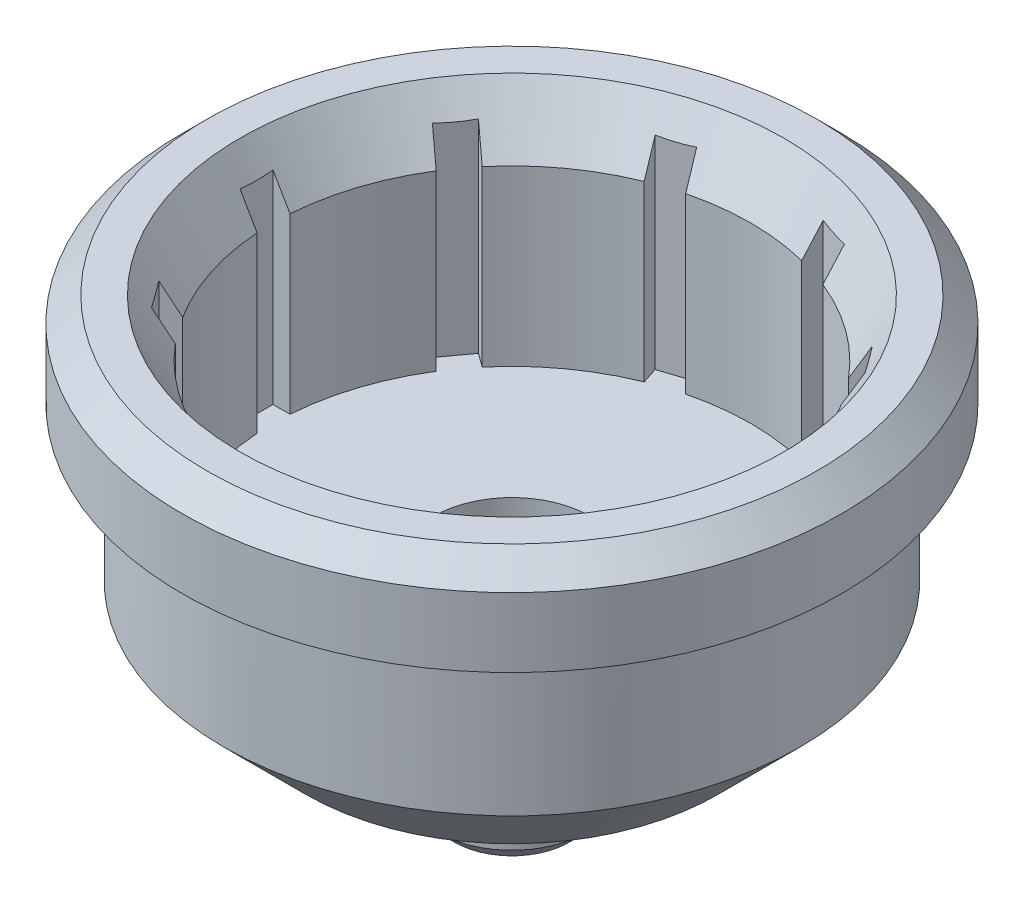
SolidWorks part; units mm, degrees
ref_plane "Front Plane" through (0, 0, 0) normal (0, 0, 1) x (1, 0, 0)
ref_plane "Top Plane" through (0, 0, 0) normal (0, 1, 0) x (1, 0, 0)
ref_plane "Right Plane" through (0, 0, 0) normal (1, 0, 0) x (0, 0, -1)
sketch "Sketch1" plane through (0, 0, 0) normal (0, 0, 1) x (1, 0, 0)
  line L0 (0, 0) -> (-2.5, 0) construction
  line L1 (-2.5, 0) -> (-2.5, 9)
  line L2 (-2.5, 9) -> (-4.75, 9)
  line L3 (-4.75, 9) -> (-4.75, 13)
  line L4 (-4.75, 13) -> (-14.5, 13)
  line L5 (-14.5, 13) -> (-14.5, 27)
  line L6 (-14.5, 27) -> (-20, 27)
  line L7 (-20, 27) -> (-20, 21.3)
  line L8 (-20, 21.3) -> (-17.5, 21.3)
  line L9 (-17.5, 21.3) -> (-17.5, 7)
  line L10 (-17.5, 7) -> (-6.5, 7)
  line L11 (-6.5, 7) -> (-6.5, 6)
  line L12 (-6.5, 6) -> (-4.5, 6)
  line L13 (-4.5, 6) -> (-4.5, 0)
  line L14 (-4.5, 0) -> (-2.5, 0)
  line L15 (0, 0) -> (0, 40) construction
  dimension "D1" = 5
  dimension "D2" = 9
  dimension "D3" = 2
  dimension "D4" = 6
  dimension "D5" = 9.5
  dimension "D6" = 4
  dimension "D7" = 3
  dimension "D8" = 1
  dimension "D9" = 29
  dimension "D10" = 35
  dimension "D11" = 40
  dimension "D12" = 5.7
  dimension "D13" = 14
revolve "Revolve1" add sketch "Sketch1" angle 360 about L15
chamfer "Chamfer1" distance 2 angle 60 1 edges at (0, 27, -14.5)
chamfer "Chamfer2" distance 1.5 angle 45 1 edges at (0, 27, -20)
sketch "Sketch2" plane through (0, 13, 0) normal (0, 1, 0) x (1, 0, 0)
  line L1 (-15.5, -1) -> (15.5, -1)
  line L2 (-15.5, -1) -> (-15.5, 1)
  line L3 (-15.5, 1) -> (15.5, 1)
  line L4 (15.5, -1) -> (15.5, 1)
  line L5 (-15.5, -1) -> (15.5, 1) construction
  line L6 (-15.5, 1) -> (15.5, -1) construction
  point P0 (0, 0)
  dimension "D1" = 2
  dimension "D2" = 31
extrude "Cut-Extrude1" cut sketch "Sketch2" along normal through all
pattern_circular "CirPattern1" count 10 over 360 about axis through (0, 0, 0) along (0, 1, 0) of "Cut-Extrude1"
chamfer "Chamfer3" distance 5 angle 45 1 edges at (0, 7, -17.5)
chamfer "Chamfer4" distance 1 angle 45 1 edges at (0, 0, -4.5)
